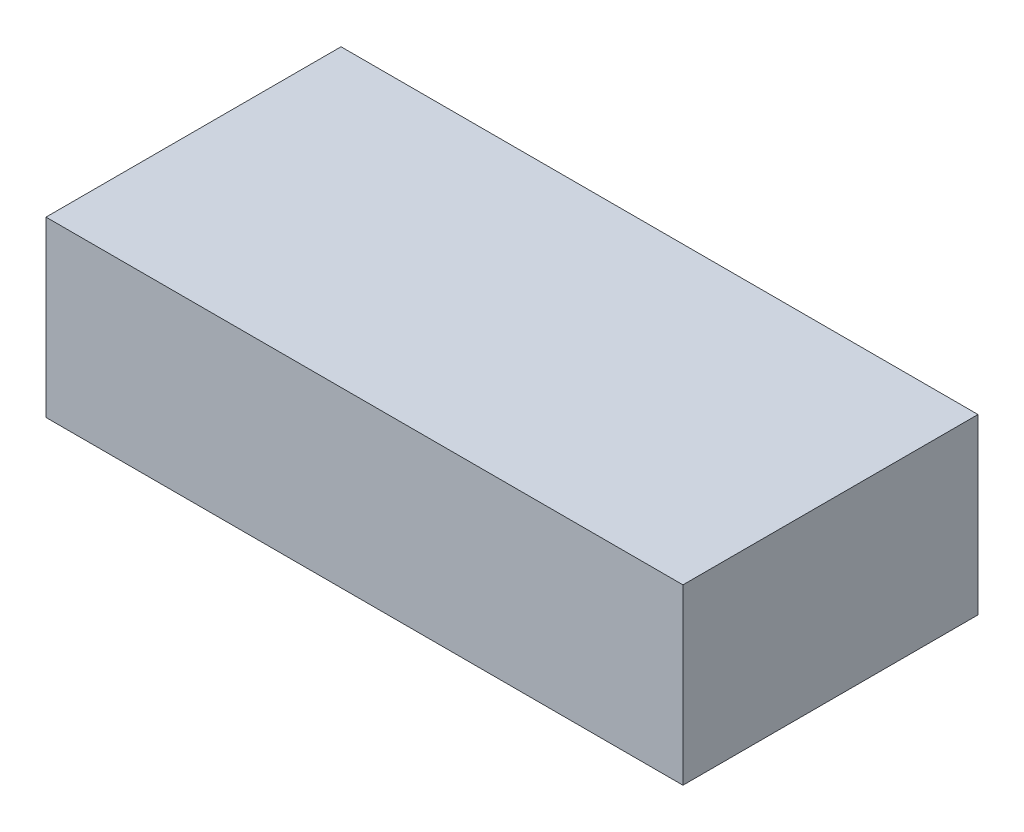
SolidWorks part; units mm, degrees
ref_plane "Front Plane" through (0, 0, 0) normal (0, 0, 1) x (1, 0, 0)
ref_plane "Top Plane" through (0, 0, 0) normal (0, 1, 0) x (1, 0, 0)
ref_plane "Right Plane" through (0, 0, 0) normal (1, 0, 0) x (0, 0, -1)
sketch "Sketch1" plane through (0, 0, 0) normal (0, 1, 0) x (1, 0, 0)
  line L1 (7.6936, 27.5306) -> (44.3936, 27.5306)
  line L2 (7.6936, 27.5306) -> (7.6936, 10.5306)
  line L3 (7.6936, 10.5306) -> (44.3936, 10.5306)
  line L4 (44.3936, 27.5306) -> (44.3936, 10.5306)
  line L5 (7.6936, 27.5306) -> (44.3936, 10.5306) construction
  line L6 (7.6936, 10.5306) -> (44.3936, 27.5306) construction
  point P0 (26.0436, 19.0306)
  dimension "D1" = 17
  dimension "D2" = 36.7
extrude "Boss-Extrude1" add sketch "Sketch1" along normal blind 10
